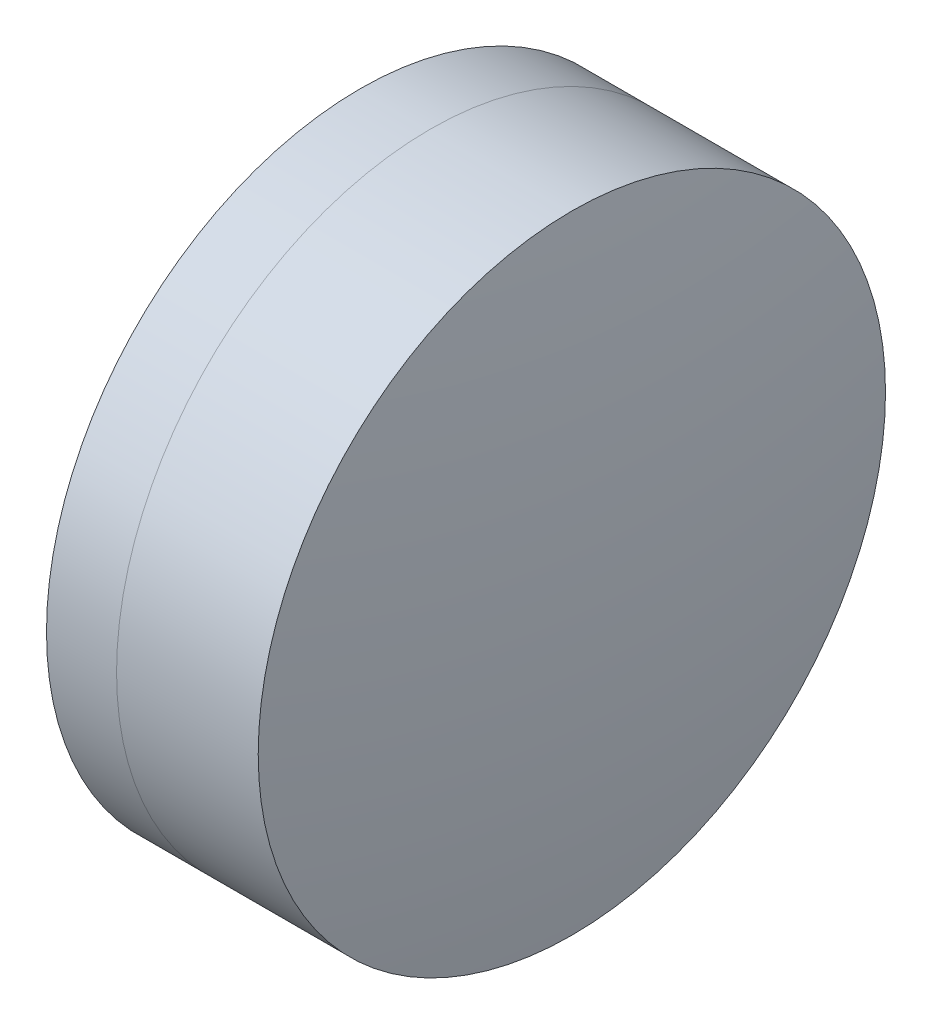
SolidWorks part; units mm, degrees
ref_plane "前视基准面" through (0, 0, 0) normal (0, 0, 1) x (1, 0, 0)
ref_plane "上视基准面" through (0, 0, 0) normal (0, 1, 0) x (1, 0, 0)
ref_plane "右视基准面" through (0, 0, 0) normal (1, 0, 0) x (0, 0, -1)
sketch "草图1" plane through (0, 0, 0) normal (0, 1, 0) x (1, 0, 0)
  line L0 (-9.7026, 0) -> (11.7646, 0) construction
  line L1 (2.6054, -5) -> (3.7223, -5)
  line L2 (2.6054, 5) -> (3.7223, 5)
  arc A0 (3.7223, -5) -> (3.7223, 5) centre (-6.6394, 0) ccw
  arc A1 (2.6054, 5) -> (2.6054, -5) centre (18.0376, 0) ccw
  point P10 (1.8156, 0)
  point P11 (4.8656, 0)
  dimension "D3" = 16.222
  dimension "D4" = 11.505
  dimension "D1" = 5
  dimension "D2" = 5
  dimension "D5" = 3.05
revolve "旋转1" add sketch "草图1" angle 360 about L0
sketch "草图2" plane through (0, 0, 0) normal (0, 1, 0) x (1, 0, 0)
  line L0 (-0.5519, 0) -> (13.3053, 0) construction
  line L2 (3.7223, 5) -> (5.9805, 5)
  line L3 (3.7223, -5) -> (5.9805, -5)
  arc A0 (5.9805, -5) -> (5.9805, 5) centre (-26.2854, 0) ccw
  arc A1 (3.7223, -5) -> (3.7223, 5) centre (-6.6394, 0) ccw construction
  arc A2 (3.7223, -5) -> (3.7223, 5) centre (-6.6394, 0) ccw
  point P4 (4.8656, 0)
  point P8 (6.3656, 0)
  dimension "D1" = 32.651
  dimension "D2" = 1.5
revolve "旋转3" add sketch "草图2" angle 360 about L0
